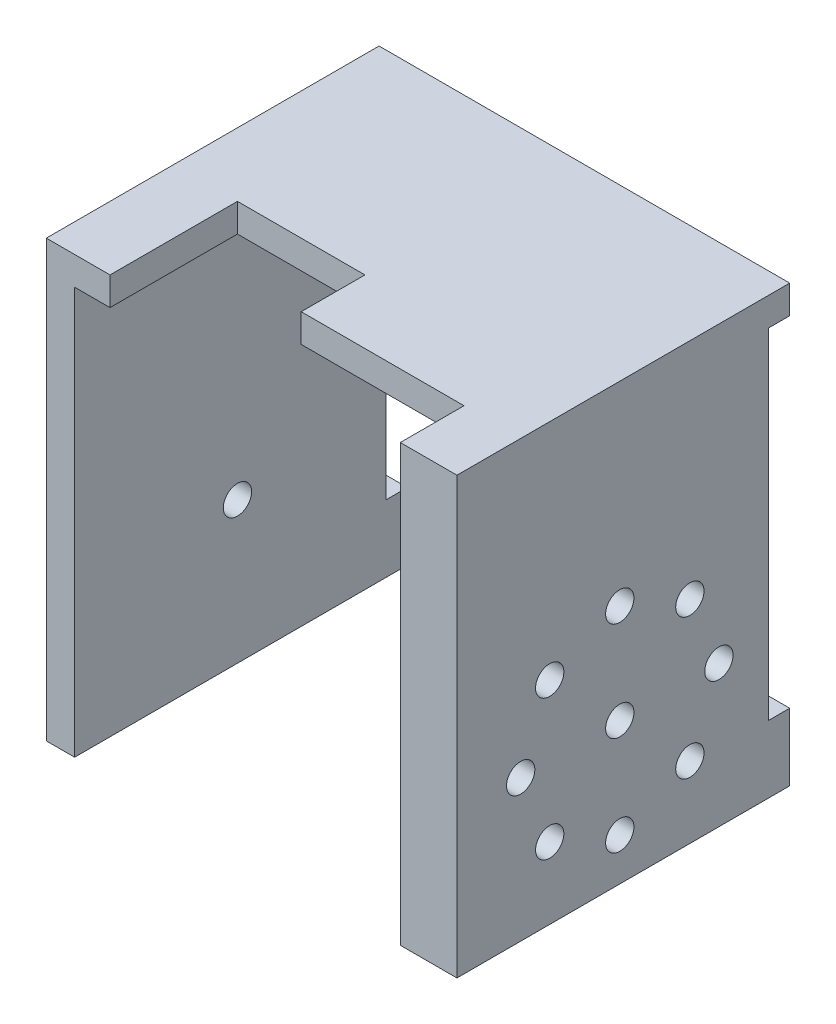
SolidWorks part; units mm, degrees
ref_plane "Plan de face" through (0, 0, 0) normal (0, 0, 1) x (1, 0, 0)
ref_plane "Plan de dessus" through (0, 0, 0) normal (0, 1, 0) x (1, 0, 0)
ref_plane "Plan de droite" through (0, 0, 0) normal (1, 0, 0) x (0, 0, -1)
sketch "Esquisse1" plane through (0, 0, 0) normal (0, 0, 1) x (1, 0, 0)
  line L0 (0, -20) -> (0, 37.5)
  line L1 (0, 37.5) -> (46, 37.5)
  line L3 (-4, -20) -> (-4, 41.5)
  line L4 (-4, 41.5) -> (54, 41.5)
  line L5 (54, 41.5) -> (54, -20)
  line L6 (0, 0) -> (0, 37.5) construction
  line L7 (0, -20) -> (-4, -20)
  line L8 (46, -20) -> (54, -20)
  line L9 (-4, 0) -> (-4, 41.5) construction
  line L10 (50, 37.5) -> (50, 0) construction
  line L11 (54, 41.5) -> (54, 0) construction
  line L12 (46, 37.5) -> (46, -20)
  line L13 (0, 37.5) -> (50, 37.5) construction
extrude "Extrusion1" add sketch "Esquisse1" along normal blind 47
sketch "Esquisse2" plane through (54, 0, 0) normal (1, 0, 0) x (0, 0, -1)
  line L3 (0, -20) -> (0, 41.5) construction
  line L4 (0, 37.5) -> (-3, 37.5)
  line L5 (-3, 37.5) -> (-3, -10.5)
  line L6 (-3, -10.5) -> (0, -10.5)
  line L7 (0, -10.5) -> (0, 37.5)
  circle A0 centre (-24, 0) radius 2
  dimension "D2" = 4
  dimension "D1" = 24
  dimension "D3" = 48
  dimension "D4" = 3
extrude "Extrusion2" cut sketch "Esquisse2" against normal through all
sketch "Esquisse3" plane through (54, 0, 0) normal (1, 0, 0) x (0, 0, -1)
  circle A1 centre (-24, 14) radius 2
  circle A2 centre (-14.1005, 9.8995) radius 2
  circle A3 centre (-10, 0) radius 2
  circle A4 centre (-14.1005, -9.8995) radius 2
  circle A5 centre (-24, -14) radius 2
  circle A6 centre (-33.8995, -9.8995) radius 2
  circle A7 centre (-38, 0) radius 2
  circle A8 centre (-33.8995, 9.8995) radius 2
extrude "Extrusion3" cut sketch "Esquisse3" against normal up to next
sketch "Esquisse4" plane through (0, 37.5, 0) normal (0, -1, 0) x (1, 0, 0)
  line L1 (5, 47) -> (5, 29)
  line L2 (0, 47) -> (46, 47) construction
  line L3 (5, 47) -> (23, 47)
  line L4 (23, 38) -> (23, 29)
  line L5 (5, 29) -> (23, 29)
  line L6 (0, 47) -> (0, 0) construction
  line L7 (23, 38) -> (46, 38)
  line L8 (46, 47) -> (46, 3) construction
  line L9 (46, 38) -> (46, 47)
  line L10 (46, 47) -> (23, 47)
  dimension "D1" = 18
  dimension "D2" = 5
  dimension "D3" = 18
extrude "Extrusion4" cut sketch "Esquisse4" against normal through all
